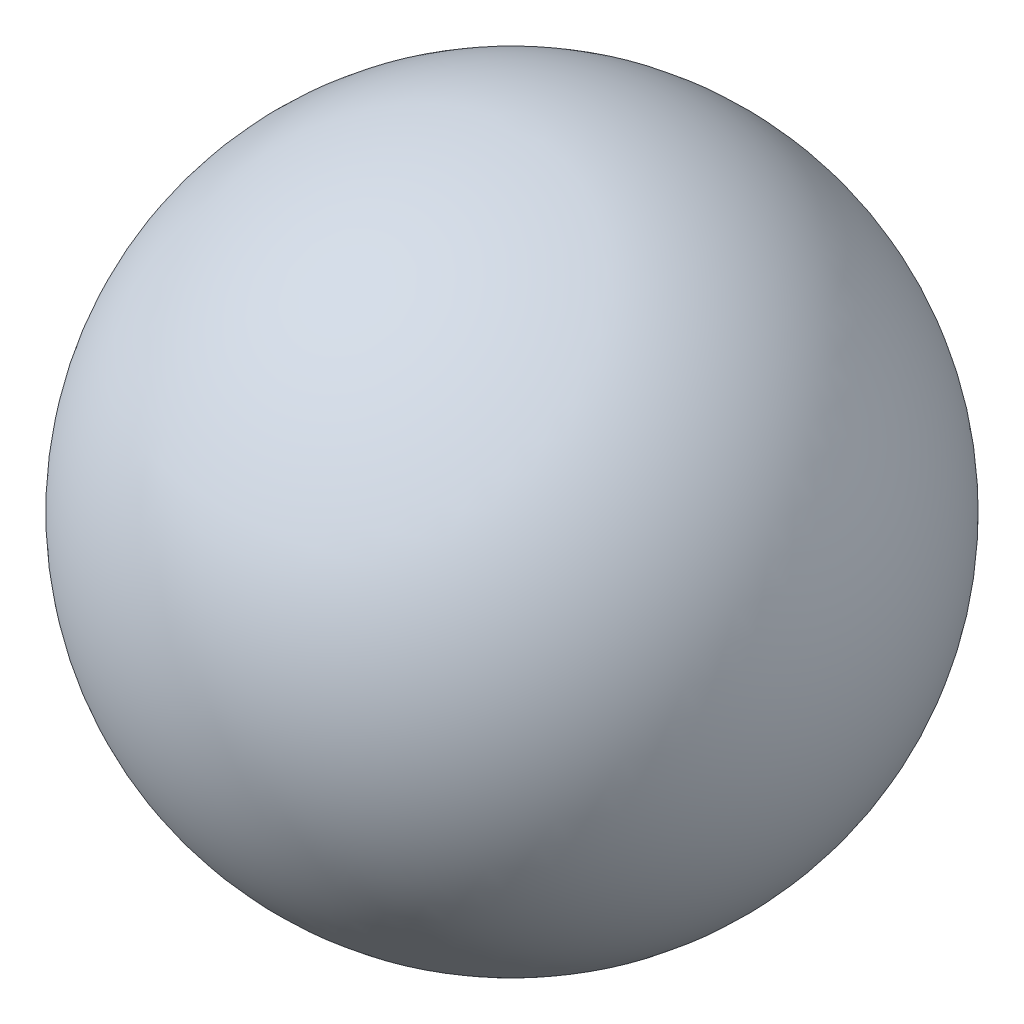
SolidWorks part; units mm, degrees
ref_plane "Ebene vorne" through (0, 0, 0) normal (0, 0, 1) x (1, 0, 0)
ref_plane "Ebene oben" through (0, 0, 0) normal (0, 1, 0) x (1, 0, 0)
ref_plane "Ebene rechts" through (0, 0, 0) normal (1, 0, 0) x (0, 0, -1)
sketch "Skizze1" plane through (0, 0, 0) normal (0, 0, 1) x (1, 0, 0)
  line L0 (0, 0) -> (0, 8.7923) construction
  line L1 (0, -55) -> (0, 55) construction
  line L2 (0, 2.5) -> (0, -2.5)
  arc A0 (0, 2.5) -> (0, -2.5) centre (0, 0) ccw
  dimension "D1" = 5
revolve "Shpere" add sketch "Skizze1" angle 360 about L0
sketch3d "somewhere on the outside"
  line L0 (0, 0, 0) -> (-1.7823, 1.6683, -0.5386)
  point P3 (0, 0, 0)
  point P4 (-1.9114, 1.5295, -0.5072)
  point P5 (-1.7646, 0.8376, -1.5604)
  point P6 (-1.7823, 1.6683, -0.5386)
ref_plane "plane" through (-1.7823, 1.6683, -0.5386) normal (-0.7129, 0.6673, -0.2155) x (-0.188, 0.1141, 0.9755)
sketch "add random complexity" plane through (-1.7823, 1.6683, -0.5386) normal (-0.7129, 0.6673, -0.2155) x (-0.188, 0.1141, 0.9755)
  line L0 (0, 0) -> (0.393, 0.7325)
  line L1 (0.393, 0.7325) -> (-0.9902, 0.4462)
  line L2 (0.393, 0.7325) -> (0.2882, 1.2384)
  point P1 (0.1553, 0.9397)
  point P3 (-0.8841, -0.0661)
  point P7 (0.2882, 1.2384)
  point P8 (0.393, 0.7325)
sketch "NACA" plane through (-1.7823, 1.6683, -0.5386) normal (-0.7129, 0.6673, -0.2155) x (-0.188, 0.1141, 0.9755)
  line L0 (0.393, 0.7325) -> (1.3722, 0.9353) construction
  line L1 (0.393, 0.7325) -> (-0.9902, 0.4462) construction
  spline S0 degree 4 poles (0.393, 0.7325) (0.3925, 0.7347) (0.3919, 0.7386) (0.3915, 0.7444) (0.392, 0.752) (0.3934, 0.7595) (0.3958, 0.7675) (0.3997, 0.7762) (0.4053, 0.7859) (0.4135, 0.7968) (0.4252, 0.8092) (0.4413, 0.823) (0.4637, 0.8384) (0.4919, 0.8541) (0.5318, 0.872) (0.5847, 0.8902) (0.6478, 0.9064) (0.7219, 0.9198) (0.7975, 0.9296) (0.8746, 0.9363) (0.95, 0.9407) (1.0286, 0.9431) (1.102, 0.9442) (1.1841, 0.9433) (1.2518, 0.9419) (1.3358, 0.9378) (1.3822, 0.9348) (1.4287, 0.931) (1.4593, 0.9282) (1.4676, 0.9272) (1.4767, 0.9264) knots 0 0 0 0 0 0.007628 0.013608 0.019719 0.026326 0.033718 0.042222 0.0524 0.064845 0.080509 0.100608 0.125283 0.158248 0.191213 0.25105 0.31698 0.38291 0.44884 0.51477 0.5807 0.64663 0.71256 0.77849 0.844419 0.910349 0.955175 0.977587 1 1 1 1 1 construction
  spline S1 degree 4 poles (0.393, 0.7325) (0.3925, 0.7347) (0.3919, 0.7386) (0.3915, 0.7444) (0.392, 0.752) (0.3934, 0.7595) (0.3958, 0.7675) (0.3997, 0.7762) (0.4053, 0.7859) (0.4135, 0.7968) (0.4252, 0.8092) (0.4413, 0.823) (0.4637, 0.8384) (0.4919, 0.8541) (0.5318, 0.872) (0.5847, 0.8902) (0.6478, 0.9064) (0.7219, 0.9198) (0.7975, 0.9296) (0.8746, 0.9363) (0.95, 0.9407) (1.0286, 0.9431) (1.102, 0.9442) (1.1841, 0.9433) (1.2518, 0.9419) (1.3203, 0.9385) (1.3548, 0.9365) (1.3722, 0.9353) knots 0 0 0 0 0 0.007628 0.013608 0.019719 0.026326 0.033718 0.042222 0.0524 0.064845 0.080509 0.100608 0.125283 0.158248 0.191213 0.25105 0.31698 0.38291 0.44884 0.51477 0.5807 0.64663 0.71256 0.77849 0.844419 0.910349 0.910349 0.910349 0.910349 0.910349
  point P0 (0.0228, 0.2473)
